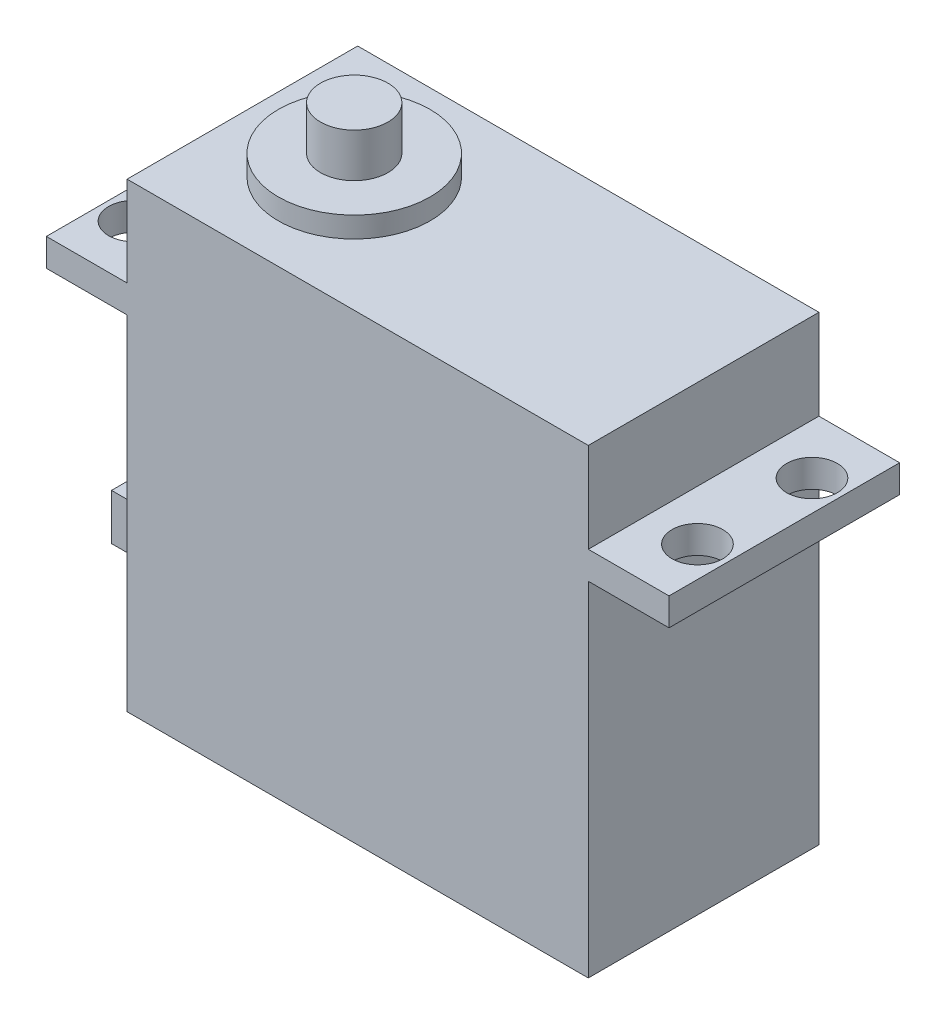
SolidWorks part; units mm, degrees
ref_plane "前视基准面" through (0, 0, 0) normal (0, 0, 1) x (1, 0, 0)
ref_plane "上视基准面" through (0, 0, 0) normal (0, 1, 0) x (1, 0, 0)
ref_plane "右视基准面" through (0, 0, 0) normal (1, 0, 0) x (0, 0, -1)
sketch "草图1" plane through (0, 0, 0) normal (0, 0, 1) x (1, 0, 0)
  line L1 (-20, -20) -> (20, -20)
  line L2 (-20, -20) -> (-20, 20)
  line L3 (-20, 20) -> (20, 20)
  line L4 (20, -20) -> (20, 20)
  line L5 (-20, -20) -> (20, 20) construction
  line L6 (-20, 20) -> (20, -20) construction
  point P0 (0, 0)
  dimension "D1" = 40
  dimension "D2" = 40
extrude "凸台-拉伸1" add sketch "草图1" along normal blind 20
sketch "草图2" plane through (0, 20, 0) normal (0, 1, 0) x (1, 0, 0)
  line L0 (-20, -20) -> (-20, 0) construction
  line L1 (-20, -10) -> (7.8989, -10) construction
  circle A0 centre (-10.3, -10) radius 6.58
  dimension "D1" = 13.16
  dimension "D2" = 9.7
extrude "凸台-拉伸2" add sketch "草图2" along normal blind 1.8
sketch "草图3" plane through (0, 21.8, 0) normal (0, 1, 0) x (1, 0, 0)
  circle A0 centre (-10.3, -10) radius 2.925
  dimension "D1" = 5.85
extrude "凸台-拉伸3" add sketch "草图3" along normal blind 3.8
ref_plane "基准面1" through (0, 12.2, 0) normal (0, 1, 0) x (1, 0, 0)
sketch "草图4" plane through (0, 12.2, 0) normal (0, 1, 0) x (1, 0, 0)
  line L0 (20, -20) -> (-20, -20) construction
  line L1 (-20, 0) -> (-27, 0)
  line L2 (-20, 0) -> (-20, -20)
  line L3 (-20, -20) -> (-27, -20)
  line L4 (-27, 0) -> (-27, -20)
  line L6 (20, 0) -> (27, 0)
  line L7 (20, 0) -> (20, -20)
  line L8 (20, -20) -> (27, -20)
  line L9 (27, 0) -> (27, -20)
  dimension "D1" = 7
  dimension "D2" = 7
extrude "凸台-拉伸4" add sketch "草图4" against normal blind 2.4
hole_wizard "Ø4.4 (4.4) 直径孔1" positions "草图5" profile "草图6" hole size "Ø4.4" standard "ISO" end condition through all
sketch "草图5" plane through (0, 12.2, 0) normal (0, 1, 0) x (1, 0, 0)
  line L0 (0, 0) -> (0, -26.0101) construction
  line L3 (-27, -10) -> (29.9804, -10) construction
  line L4 (-27, 0) -> (-27, -20) construction
  point P0 (-24.35, -4.95)
  point P2 (-24.35, -15.05)
  point P4 (24.35, -4.95)
  point P6 (24.35, -14.884)
  dimension "D1" = 48.7
  dimension "D2" = 10.1
sketch "草图6" plane through (-24.35, 12.2, 4.95) normal (1, 0, 0) x (0, 0, 1)
  line L0 (0, 0) -> (0, 32.2)
  line L1 (0, 32.2) -> (2.2, 32.2)
  line L2 (2.2, 32.2) -> (2.2, 0)
  line L5 (2.2, 0) -> (0, 0)
  line L11 (0, -6.35) -> (0, 107.95) construction
  dimension "通孔孔直径" = 4.4
  dimension "通孔孔深度" = 32.2
sketch "草图7" plane through (-20, 0, 0) normal (-1, 0, 0) x (0, 0, 1)
  line L0 (20, -20) -> (0, -20) construction
  line L1 (7.15, -15.2) -> (12.85, -15.2)
  line L2 (7.15, -15.2) -> (7.15, -11.2)
  line L3 (7.15, -11.2) -> (12.85, -11.2)
  line L4 (12.85, -15.2) -> (12.85, -11.2)
  line L5 (10, -20) -> (10, -3.3883) construction
  dimension "D1" = 8.8
  dimension "D2" = 5.7
  dimension "D3" = 4
extrude "凸台-拉伸5" add sketch "草图7" along normal blind 8.5
